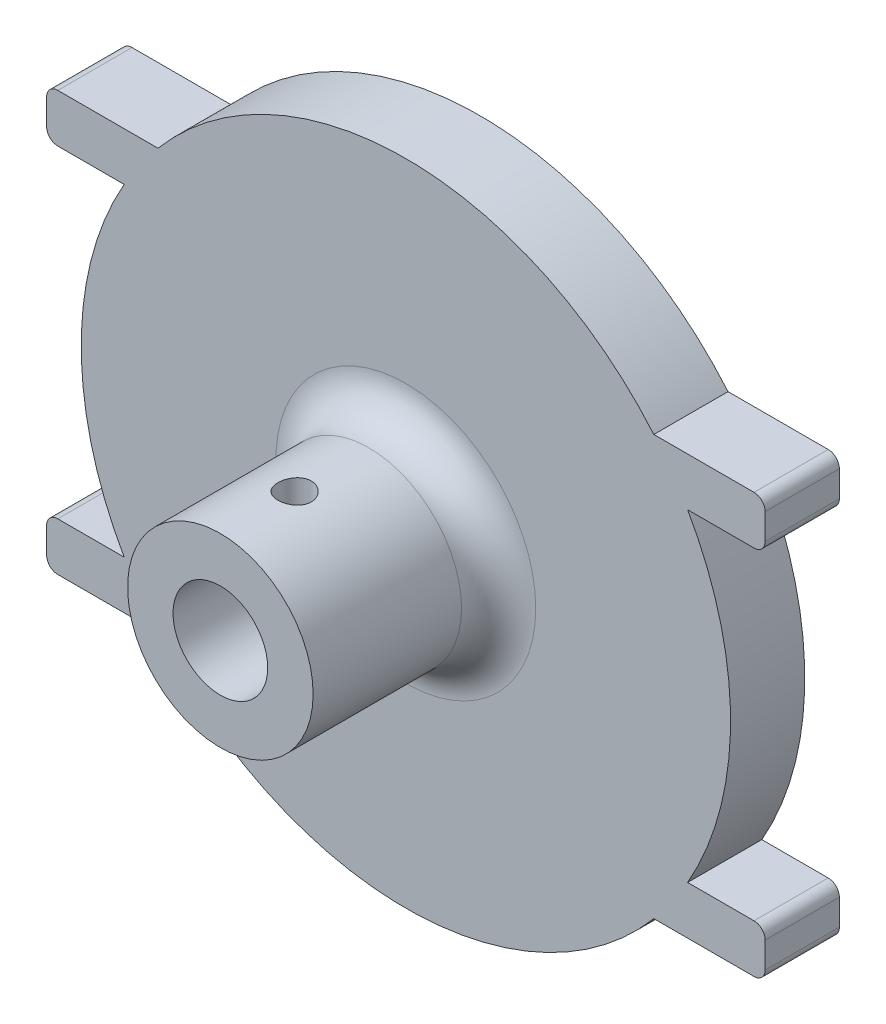
SolidWorks part; units mm, degrees
ref_plane "Front Plane" through (0, 0, 0) normal (0, 0, 1) x (1, 0, 0)
ref_plane "Top Plane" through (0, 0, 0) normal (0, 1, 0) x (1, 0, 0)
ref_plane "Right Plane" through (0, 0, 0) normal (1, 0, 0) x (0, 0, -1)
sketch "Sketch1" plane through (0, 0, 0) normal (0, 0, 1) x (1, 0, 0)
  line L0 (-23.8285, 14.351) -> (-16.9705, 14.351)
  line L1 (24.5905, 13.589) -> (24.5905, 11.811)
  line L2 (23.8285, 11.049) -> (19.2839, 11.049)
  line L3 (-24.5905, 11.811) -> (-24.5905, 13.589)
  line L4 (-19.2839, 11.049) -> (-23.8285, 11.049)
  line L5 (16.9705, 14.351) -> (23.8285, 14.351)
  line L6 (-22.225, 0) -> (22.225, 0) construction
  line L7 (23.8285, -11.049) -> (19.2839, -11.049)
  line L8 (24.5905, -13.589) -> (24.5905, -11.811)
  line L9 (16.9705, -14.351) -> (23.8285, -14.351)
  line L10 (-23.8285, -14.351) -> (-16.9705, -14.351)
  line L11 (-24.5905, -11.811) -> (-24.5905, -13.589)
  line L12 (-19.2839, -11.049) -> (-23.8285, -11.049)
  arc A0 (-19.2839, 11.049) -> (-19.2839, -11.049) centre (0, 0) ccw
  arc A1 (23.8285, 14.351) -> (24.5905, 13.589) centre (23.8285, 13.589) cw
  arc A2 (24.5905, 11.811) -> (23.8285, 11.049) centre (23.8285, 11.811) cw
  arc A3 (23.8285, -11.049) -> (24.5905, -11.811) centre (23.8285, -11.811) cw
  arc A4 (24.5905, -13.589) -> (23.8285, -14.351) centre (23.8285, -13.589) cw
  arc A5 (-23.8285, -14.351) -> (-24.5905, -13.589) centre (-23.8285, -13.589) cw
  arc A6 (-24.5905, -11.811) -> (-23.8285, -11.049) centre (-23.8285, -11.811) cw
  arc A7 (-23.8285, 11.049) -> (-24.5905, 11.811) centre (-23.8285, 11.811) cw
  arc A8 (-23.8285, 14.351) -> (-24.5905, 13.589) centre (-23.8285, 13.589) ccw
  arc A9 (-16.9705, -14.351) -> (16.9705, -14.351) centre (0, 0) ccw
  arc A10 (19.2839, -11.049) -> (19.2839, 11.049) centre (0, 0) ccw
  arc A11 (16.9705, 14.351) -> (-16.9705, 14.351) centre (0, 0) ccw
  point P23 (24.5905, 14.351)
  point P26 (24.5905, 11.049)
  point P29 (24.5905, -11.049)
  point P32 (24.5905, -14.351)
  point P35 (-24.5905, -14.351)
  point P38 (-24.5905, -11.049)
  point P41 (-24.5905, 11.049)
  point P44 (-24.5905, 14.351)
  dimension "D1" = 44.45
  dimension "D7" = 0.762
  dimension "D2" = 3.302
  dimension "D3" = 7.62
  dimension "D4" = 7.62
  dimension "D5" = 3.302
  dimension "D6" = 22.098
extrude "Boss-Extrude1" add sketch "Sketch1" along normal blind 5.08
sketch "Sketch5" plane through (0, 0, 0) normal (0, 0, -1) x (-1, 0, 0)
  circle A0 centre (0, 0) radius 9.6901
  dimension "D1" = 19.3802
extrude "Cut-Extrude2" cut sketch "Sketch5" against normal blind 2.54
sketch "Sketch6" plane through (0, 0, 5.08) normal (0, 0, 1) x (1, 0, 0)
  circle A0 centre (0, 0) radius 6.35
  circle A1 centre (0, 0) radius 3.2385
  dimension "D1" = 12.7
  dimension "D2" = 6.477
extrude "Boss-Extrude4" add sketch "Sketch6" along normal blind 12.7
fillet "Fillet1" radius 2.54 1 edges at (6.35, 0, 5.08)
ref_plane "Plane1" through (0, 6.35, 0) normal (0, 1, 0) x (1, 0, 0)
sketch "Sketch8" plane through (0, 6.35, 0) normal (0, 1, 0) x (1, 0, 0)
  line L0 (-6.35, -17.78) -> (6.35, -17.78) construction
  circle A0 centre (0, -12.7) radius 1.143
  dimension "D1" = 2.286
  dimension "D2" = 5.08
extrude "Cut-Extrude3" cut sketch "Sketch8" against normal blind 7.62
sketch "Sketch9" plane through (0, 0, 2.54) normal (0, 0, -1) x (-1, 0, 0)
  circle A0 centre (0, 0) radius 1.905
  dimension "D1" = 3.81
extrude "Cut-Extrude4" cut sketch "Sketch9" against normal through all
